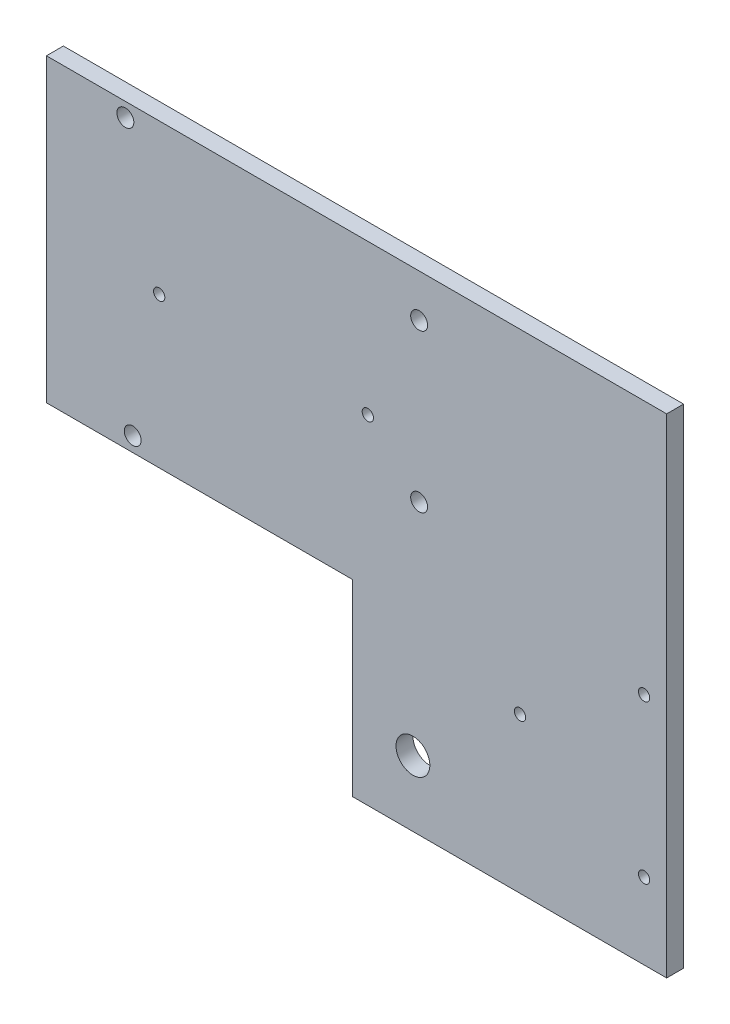
SolidWorks part; units mm, degrees
ref_plane "Front Plane" through (0, 0, 0) normal (0, 0, 1) x (1, 0, 0)
ref_plane "Top Plane" through (0, 0, 0) normal (0, 1, 0) x (1, 0, 0)
ref_plane "Right Plane" through (0, 0, 0) normal (1, 0, 0) x (0, 0, -1)
sketch "Model" plane through (0, 0, 0) normal (0, 0, 1) x (1, 0, 0)
  line L0 (26.5899, 98.9181) -> (26.5899, 45.6181)
  line L1 (26.5899, 45.6181) -> (80.8899, 45.6181)
  line L3 (26.5899, 98.9181) -> (136.5899, 98.9181)
  line L5 (136.5899, 98.9181) -> (136.5899, 45.6181)
  line L7 (80.8899, 12.2681) -> (80.8899, 45.6181)
  line L11 (136.5899, 12.2681) -> (80.8899, 12.2681)
  line L12 (136.5899, 45.6181) -> (136.5899, 12.2681)
  circle A0 centre (40.5899, 96.4181) radius 1.5
  circle A1 centre (92.6899, 63.4181) radius 1.5
  circle A2 centre (41.8899, 48.2181) radius 1.5
  circle A3 centre (92.6899, 91.3181) radius 1.5
  circle A4 centre (110.5899, 39.7681) radius 1
  circle A5 centre (46.5899, 72.2681) radius 1
  circle A6 centre (83.5899, 72.2681) radius 1
  circle A7 centre (132.5899, 25.7681) radius 1
  circle A8 centre (91.5899, 23.9181) radius 3
  circle A9 centre (132.5899, 53.7681) radius 1
  point P30 (40.5899, 45.6181)
  point P31 (91.5899, 98.9181)
  point P32 (110.5899, 12.2681)
  point P33 (121.5899, 12.2681)
  point P34 (132.5899, 12.2681)
  point P35 (41.8899, 45.6181)
extrude "Boss-Extrude1" add sketch "Model" along normal blind 3 contours L0 L1 L7 L11 L12 L5 L3 | A0 | A5 | A2 | A6 | A3 | A1 | A4 | A9 | A8 | A7
